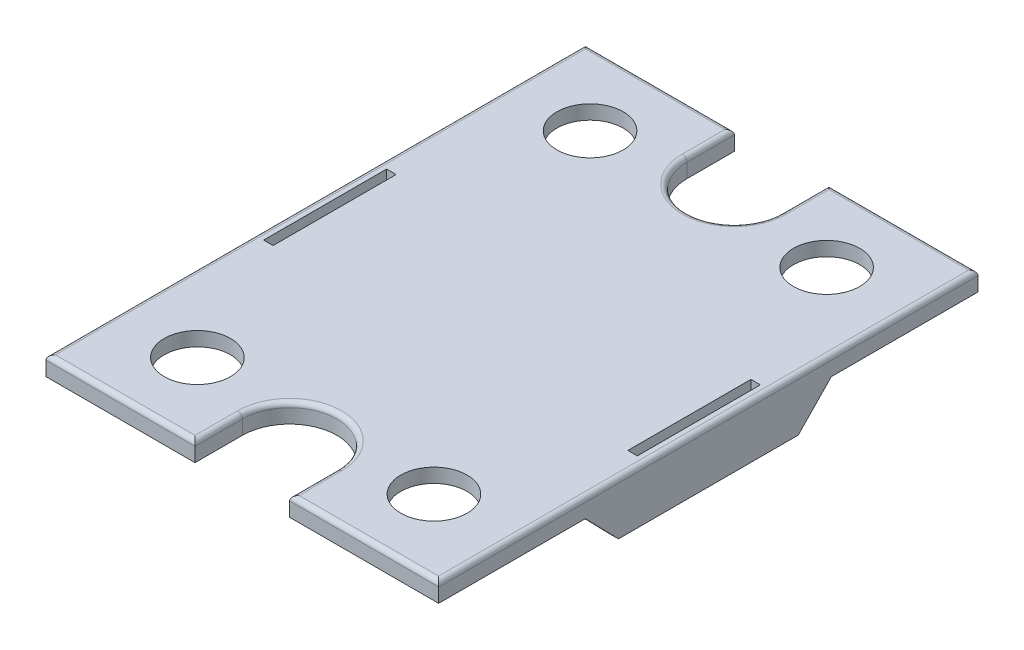
SolidWorks part; units mm, degrees
material "PBTP"
ref_plane "Front Plane" through (0, 0, 0) normal (0, 0, 1) x (1, 0, 0)
ref_plane "Top Plane" through (0, 0, 0) normal (0, 1, 0) x (1, 0, 0)
ref_plane "Right Plane" through (0, 0, 0) normal (1, 0, 0) x (0, 0, -1)
sketch "Sketch1" plane through (0, 0, 0) normal (0, 1, 0) x (1, 0, 0)
  line L1 (-20.75, 28.5) -> (20.75, 28.5)
  line L2 (-20.75, 28.5) -> (-20.75, -28.5)
  line L3 (-20.75, -28.5) -> (20.75, -28.5)
  line L4 (20.75, 28.5) -> (20.75, -28.5)
  line L5 (-20.75, 28.5) -> (20.75, -28.5) construction
  line L6 (-20.75, -28.5) -> (20.75, 28.5) construction
  point P0 (0, 0)
  dimension "D1" = 41.5
  dimension "D2" = 57
extrude "Boss-Extrude1" add sketch "Sketch1" along normal blind 2
sketch "Sketch2" plane through (0, 2, 0) normal (0, 1, 0) x (1, 0, 0)
  line L0 (0, 0) -> (0, -28.5) construction
  line L1 (-20.75, -28.5) -> (20.75, -28.5) construction
  line L3 (-5, -23.5) -> (5, -23.5) construction
  line L4 (-5, -23.5) -> (-5, -28.5)
  line L5 (-5, -28.5) -> (5, -28.5)
  line L6 (5, -23.5) -> (5, -28.5)
  line L7 (-5, -23.5) -> (5, -28.5) construction
  line L8 (-5, -28.5) -> (5, -23.5) construction
  arc A0 (-5, -23.5) -> (5, -23.5) centre (0, -23.5) cw
  point P5 (0, -26)
  dimension "D1" = 10
  dimension "D2" = 5
extrude "Cut-Extrude1" cut sketch "Sketch2" against normal through all
sketch "Sketch3" plane through (0, 2, 0) normal (0, 1, 0) x (1, 0, 0)
  line L0 (-20.75, -28.5) -> (-5, -28.5) construction
  line L1 (-20.75, 28.5) -> (-20.75, -28.5) construction
  line L2 (0, 0) -> (0, -28.5) construction
  line L3 (0, -28.5) -> (-5, -28.5) construction
  circle A0 centre (-12.5, -20.75) radius 3.5
  circle A1 centre (12.5, -20.75) radius 3.5
  dimension "D1" = 7
  dimension "D2" = 7.75
  dimension "D3" = 8.25
extrude "Cut-Extrude2" cut sketch "Sketch3" against normal through all
mirror "Mirror1" about plane through (0, 0, 0) normal (0, 0, 1) of "Cut-Extrude2", "Cut-Extrude1"
sketch "Sketch4" plane through (0, 2, 0) normal (0, 1, 0) x (1, 0, 0)
  line L0 (0, 0) -> (-19.75, 0) construction
  line L1 (-20.75, 28.5) -> (-20.75, -28.5) construction
  line L2 (-18.75, 6.5) -> (-20.75, 6.5)
  line L3 (-18.75, 6.5) -> (-18.75, -6.5)
  line L4 (-18.75, -6.5) -> (-20.75, -6.5)
  line L5 (-20.75, 6.5) -> (-20.75, -6.5)
  line L6 (-18.75, 6.5) -> (-20.75, -6.5) construction
  line L7 (-18.75, -6.5) -> (-20.75, 6.5) construction
  line L8 (0, 0) -> (0, -18.5) construction
  line L9 (18.75, -6.5) -> (20.75, -6.5)
  line L10 (20.75, 6.5) -> (20.75, -6.5)
  line L11 (18.75, 6.5) -> (20.75, 6.5)
  line L12 (18.75, 6.5) -> (18.75, -6.5)
  arc A0 (5, -23.5) -> (-5, -23.5) centre (0, -23.5) ccw construction
  dimension "D1" = 2
  dimension "D2" = 13
extrude "Cut-Extrude3" cut sketch "Sketch4" against normal through all
sketch "Sketch5" plane through (0, 0, 0) normal (0, 1, 0) x (1, 0, 0)
  line L56 (-18.75, 26.5) -> (-18.75, 8.5)
  line L57 (-18.75, 8.5) -> (-16.75, 8.5)
  line L58 (-16.75, 8.5) -> (-16.75, -8.5)
  line L59 (-16.75, -8.5) -> (-18.75, -8.5)
  line L60 (-18.75, -8.5) -> (-18.75, -26.5)
  line L61 (-18.75, -26.5) -> (-7, -26.5)
  line L62 (-7, -26.5) -> (-7, -23.5)
  line L63 (7, -23.5) -> (7, -26.5)
  line L64 (7, -26.5) -> (18.75, -26.5)
  line L65 (18.75, -26.5) -> (18.75, -8.5)
  line L66 (18.75, -8.5) -> (16.75, -8.5)
  line L67 (16.75, -8.5) -> (16.75, 8.5)
  line L68 (16.75, 8.5) -> (18.75, 8.5)
  line L69 (18.75, 8.5) -> (18.75, 26.5)
  line L70 (18.75, 26.5) -> (7, 26.5)
  line L71 (7, 26.5) -> (7, 23.5)
  line L72 (-7, 26.5) -> (-18.75, 26.5)
  line L73 (-7, 23.5) -> (-7, 26.5)
  line L74 (-18.75, 26.5) -> (-18.75, 8.5)
  line L75 (-18.75, 8.5) -> (-16.75, 8.5)
  line L76 (-16.75, 8.5) -> (-16.75, -8.5)
  line L77 (-16.75, -8.5) -> (-18.75, -8.5)
  line L78 (-18.75, -8.5) -> (-18.75, -26.5)
  line L79 (-18.75, -26.5) -> (-7, -26.5)
  line L80 (-7, -26.5) -> (-7, -23.5)
  line L81 (7, -23.5) -> (7, -26.5)
  line L82 (7, -26.5) -> (18.75, -26.5)
  line L83 (18.75, -26.5) -> (18.75, -8.5)
  line L84 (18.75, -8.5) -> (16.75, -8.5)
  line L85 (16.75, -8.5) -> (16.75, 8.5)
  line L86 (16.75, 8.5) -> (18.75, 8.5)
  line L87 (18.75, 8.5) -> (18.75, 26.5)
  line L88 (18.75, 26.5) -> (7, 26.5)
  line L89 (7, 26.5) -> (7, 23.5)
  line L90 (-7, 26.5) -> (-18.75, 26.5)
  line L91 (-7, 23.5) -> (-7, 26.5)
  arc A8 (7, -23.5) -> (-7, -23.5) centre (0, -23.5) ccw
  arc A9 (-7, 23.5) -> (7, 23.5) centre (0, 23.5) ccw
  arc A10 (7, -23.5) -> (-7, -23.5) centre (0, -23.5) ccw
  arc A11 (-7, 23.5) -> (7, 23.5) centre (0, 23.5) ccw
  dimension "D1" = 2
extrude "Cut-Extrude4" cut sketch "Sketch5" along normal blind 0.5
sketch "Sketch6" plane through (-20.75, 0, 0) normal (-1, 0, 0) x (0, 0, 1)
  line L0 (0, 0) -> (0, 2) construction
  line L1 (-13, 2) -> (13, 2)
  line L3 (6.5, 2) -> (28.5, 2) construction
  line L6 (-13, 2) -> (-13, 0)
  line L7 (-28.5, 0) -> (-6.5, 0) construction
  line L8 (-13, 0) -> (13, 0) construction
  line L9 (6.5, 0) -> (28.5, 0) construction
  line L10 (13, 2) -> (13, 0)
  line L11 (0, 0) -> (0, -3.6) construction
  line L12 (-9.5, -3.6) -> (9.5, -3.6)
  line L13 (13, 0) -> (9.5, -3.6)
  line L14 (-13, 0) -> (-9.5, -3.6)
  point P21 (0, -3.6)
  dimension "D2" = 26
  dimension "D4" = 19
  dimension "D5" = 5.6
extrude "Boss-Extrude2" add sketch "Sketch6" against normal blind 1 contours L14 L12 L13 L10 L1 L6
sketch "Sketch7" plane through (-19.75, 0, 0) normal (1, 0, 0) x (0, 0, -1)
  line L0 (9.5, -3.6) -> (-9.5, -3.6) construction
  line L1 (-6.5, -3.6) -> (-3, -3.6)
  line L2 (-6.5, -3.6) -> (-6.5, -3)
  line L3 (-6.5, -3) -> (-3, -3)
  line L4 (-3, -3.6) -> (-3, -3)
  line L5 (-6.5, -3.6) -> (-3, -3) construction
  line L6 (-6.5, -3) -> (-3, -3.6) construction
  line L7 (-6.5, 2) -> (-6.5, 0) construction
  line L8 (0, 0) -> (0, -3.6) construction
  line L9 (6.5, -3.6) -> (6.5, -3)
  line L10 (6.5, -3.6) -> (3, -3.6)
  line L11 (3, -3.6) -> (3, -3)
  line L12 (6.5, -3) -> (3, -3)
  point P4 (-4.75, -3.3)
  dimension "D1" = 0.6
  dimension "D2" = 3.5
extrude "Boss-Extrude3" add sketch "Sketch7" along normal blind 0.3
mirror "Mirror2" about plane through (0, 0, 0) normal (1, 0, 0) of "Boss-Extrude3", "Boss-Extrude2"
fillet "Fillet1" radius 0.5 12 edges at (-5, 2, 26) (0, 2, 18.5) (5, 2, -26) (0, 2, -18.5) (5, 2, 26) (12.875, 2, 28.5) (20.75, 2, 0) (12.875, 2, -28.5) (-5, 2, -26) (-12.875, 2, -28.5) (-20.75, 2, 0) (-12.875, 2, 28.5)
